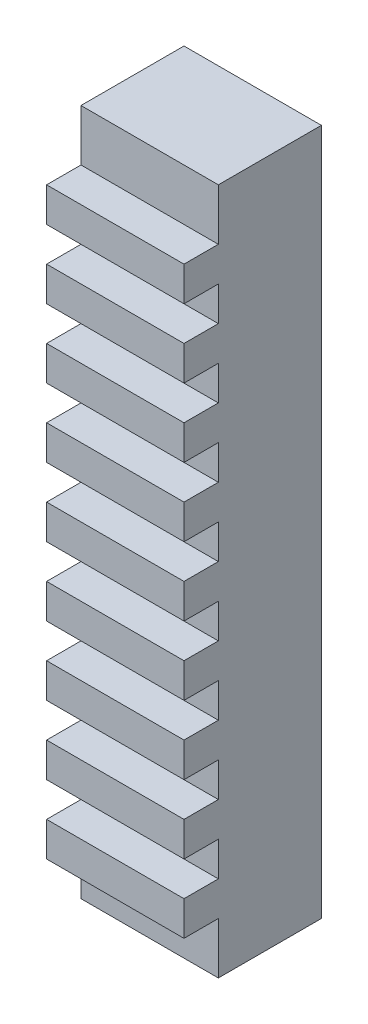
SolidWorks part; units mm, degrees
ref_plane "Front Plane" through (0, 0, 0) normal (0, 0, 1) x (1, 0, 0)
ref_plane "Top Plane" through (0, 0, 0) normal (0, 1, 0) x (1, 0, 0)
ref_plane "Right Plane" through (0, 0, 0) normal (1, 0, 0) x (0, 0, -1)
sketch "Sketch1" plane through (0, 0, 0) normal (0, 0, 1) x (1, 0, 0)
  line L1 (-10, -50) -> (10, -50)
  line L2 (-10, -50) -> (-10, 50)
  line L3 (-10, 50) -> (10, 50)
  line L4 (10, -50) -> (10, 50)
  line L5 (-10, -50) -> (10, 50) construction
  line L6 (-10, 50) -> (10, -50) construction
  point P0 (0, 0)
  dimension "D1" = 100
  dimension "D2" = 20
extrude "Boss-Extrude1" add sketch "Sketch1" along normal blind 15
sketch "Sketch2" plane through (0, 0, 15) normal (0, 0, 1) x (1, 0, 0)
  line L0 (10, -50) -> (10, 50) construction
  line L1 (-10, -2.5) -> (10, -2.5)
  line L2 (-10, -2.5) -> (-10, 2.5)
  line L3 (-10, 2.5) -> (10, 2.5)
  line L4 (10, -2.5) -> (10, 2.5)
  line L5 (-10, -2.5) -> (10, 2.5) construction
  line L6 (-10, 2.5) -> (10, -2.5) construction
  line L7 (-10, -7.5) -> (10, -7.5)
  line L8 (10, -12.5) -> (10, -7.5)
  line L9 (-10, -12.5) -> (10, -12.5)
  line L10 (-10, -12.5) -> (-10, -7.5)
  line L11 (-10, -17.5) -> (10, -17.5)
  line L12 (10, -22.5) -> (10, -17.5)
  line L13 (-10, -22.5) -> (10, -22.5)
  line L14 (-10, -22.5) -> (-10, -17.5)
  line L15 (-10, -27.5) -> (10, -27.5)
  line L16 (10, -32.5) -> (10, -27.5)
  line L17 (-10, -32.5) -> (10, -32.5)
  line L18 (-10, -32.5) -> (-10, -27.5)
  line L19 (-10, -37.5) -> (10, -37.5)
  line L20 (10, -42.5) -> (10, -37.5)
  line L21 (-10, -42.5) -> (10, -42.5)
  line L22 (-10, -42.5) -> (-10, -37.5)
  line L35 (-10, 7.5) -> (-10, 12.5)
  line L36 (-10, 7.5) -> (10, 7.5)
  line L37 (10, 7.5) -> (10, 12.5)
  line L38 (-10, 12.5) -> (10, 12.5)
  line L39 (-10, 17.5) -> (-10, 22.5)
  line L40 (-10, 17.5) -> (10, 17.5)
  line L41 (10, 17.5) -> (10, 22.5)
  line L42 (-10, 22.5) -> (10, 22.5)
  line L43 (-10, 27.5) -> (-10, 32.5)
  line L44 (-10, 27.5) -> (10, 27.5)
  line L45 (10, 27.5) -> (10, 32.5)
  line L46 (-10, 32.5) -> (10, 32.5)
  line L47 (-10, 37.5) -> (-10, 42.5)
  line L48 (-10, 37.5) -> (10, 37.5)
  line L49 (10, 37.5) -> (10, 42.5)
  line L50 (-10, 42.5) -> (10, 42.5)
  line L63 (-10, 67.5) -> (10, 67.5) [skipped]
  line L64 (-10, 67.5) -> (-10, 72.5) [skipped]
  line L65 (10, 67.5) -> (10, 72.5) [skipped]
  line L66 (-10, 72.5) -> (10, 72.5) [skipped]
  line L67 (-10, 62.5) -> (10, 62.5) [skipped]
  line L68 (-10, 57.5) -> (-10, 62.5) [skipped]
  line L69 (-10, 57.5) -> (10, 57.5) [skipped]
  line L70 (10, 57.5) -> (10, 62.5) [skipped]
  line L71 (-10, 52.5) -> (10, 52.5) [skipped]
  line L72 (-10, 47.5) -> (-10, 52.5) [skipped]
  line L73 (-10, 47.5) -> (10, 47.5) [skipped]
  line L74 (10, 47.5) -> (10, 52.5) [skipped]
  line L75 (-10, -57.5) -> (10, -57.5) [skipped]
  line L76 (-10, -62.5) -> (10, -62.5) [skipped]
  line L77 (-10, -72.5) -> (10, -72.5) [skipped]
  line L78 (10, -72.5) -> (10, -67.5) [skipped]
  line L79 (-10, -67.5) -> (10, -67.5) [skipped]
  line L80 (10, -62.5) -> (10, -57.5) [skipped]
  line L81 (-10, -62.5) -> (-10, -57.5) [skipped]
  line L82 (-10, -72.5) -> (-10, -67.5) [skipped]
  line L83 (-10, -47.5) -> (10, -47.5) [skipped]
  line L84 (-10, -52.5) -> (10, -52.5) [skipped]
  line L85 (10, -52.5) -> (10, -47.5) [skipped]
  line L86 (-10, -52.5) -> (-10, -47.5) [skipped]
  point P0 (0, 0)
  dimension "D1" = 5
  dimension "D2" = 8
  dimension "D3" = 8
extrude "Boss-Extrude2" add sketch "Sketch2" along normal blind 5
